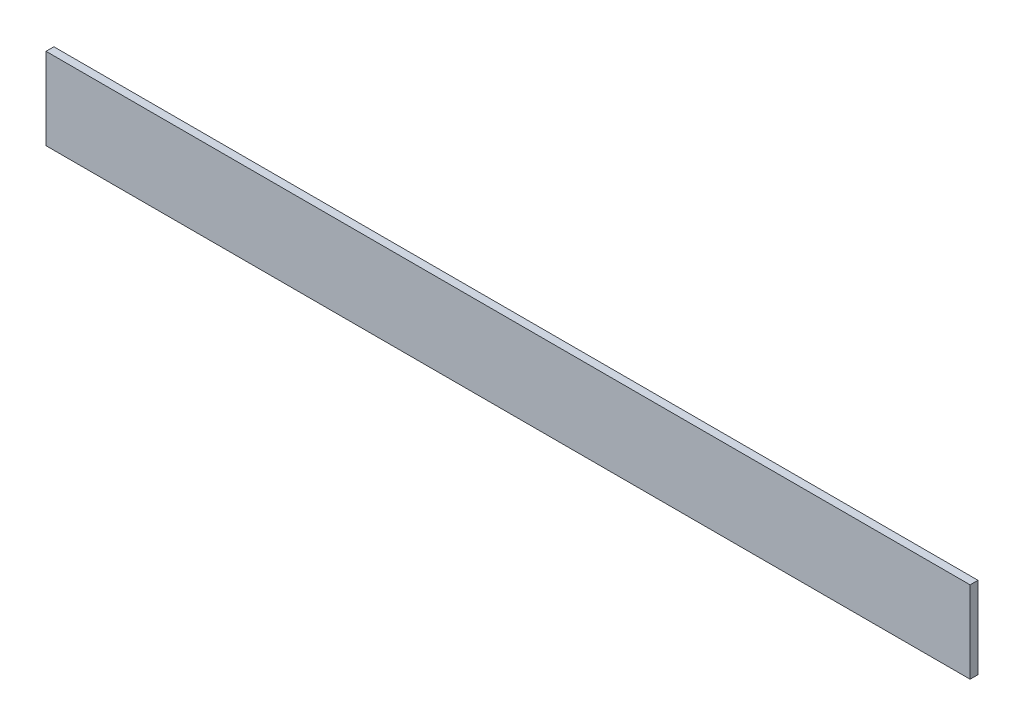
SolidWorks part; units mm, degrees
ref_plane "Plan de face" through (0, 0, 0) normal (0, 0, 1) x (1, 0, 0)
ref_plane "Plan de dessus" through (0, 0, 0) normal (0, 1, 0) x (1, 0, 0)
ref_plane "Plan de droite" through (0, 0, 0) normal (1, 0, 0) x (0, 0, -1)
sketch "Esquisse1" plane through (0, 0, 0) normal (0, 0, 1) x (1, 0, 0)
  line L1 (0, 0) -> (938, 0)
  line L2 (0, 0) -> (0, 83)
  line L3 (0, 83) -> (938, 83)
  line L4 (938, 0) -> (938, 83)
  dimension "D1" = 938
  dimension "D2" = 83
extrude "Extrusion1" add sketch "Esquisse1" against normal blind 8
